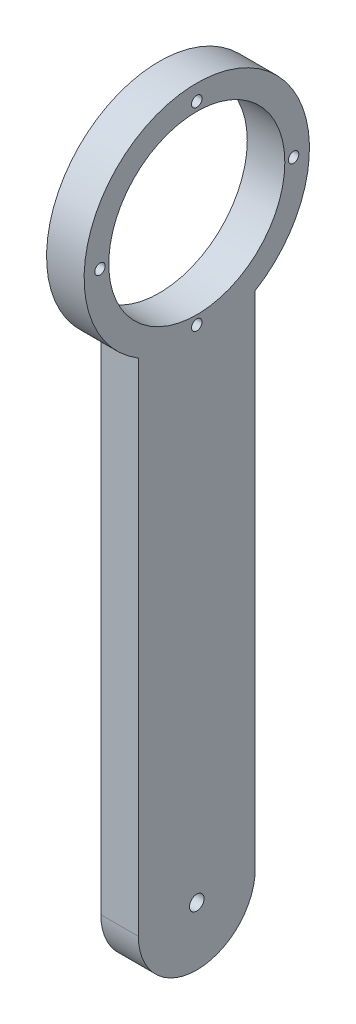
SolidWorks part; units mm, degrees
ref_plane "前视基准面" through (0, 0, 0) normal (0, 0, 1) x (1, 0, 0)
ref_plane "上视基准面" through (0, 0, 0) normal (0, 1, 0) x (1, 0, 0)
ref_plane "右视基准面" through (0, 0, 0) normal (1, 0, 0) x (0, 0, -1)
sketch "草图1" plane through (0, 0, 0) normal (1, 0, 0) x (0, 0, -1)
  line L2 (0, 0) -> (0, 120)
  line L4 (28, 0) -> (28, 120)
  arc A0 (0, 0) -> (28, 0) centre (14, 0) ccw
  arc A1 (28, 120) -> (0, 120) centre (14, 143.0868) ccw
  dimension "D3" = 27
  dimension "D1" = 28
  dimension "D2" = 120
extrude "凸台-拉伸6" add sketch "草图1" along normal blind 9
sketch "草图8" plane through (9, 0, 0) normal (1, 0, 0) x (0, 0, -1)
  circle A0 centre (14, 143.0868) radius 23.25
extrude "切除-拉伸6" cut sketch "草图8" against normal blind 7
sketch "草图9" plane through (2, 0, 0) normal (1, 0, 0) x (0, 0, -1)
  circle A0 centre (14, 143.0868) radius 19.25
extrude "切除-拉伸7" cut sketch "草图9" against normal blind 7
sketch "草图13" plane through (9, 0, 0) normal (1, 0, 0) x (0, 0, -1)
  circle A0 centre (14, 143.0868) radius 23.25
extrude "凸台-拉伸9" add sketch "草图13" against normal blind 9
sketch "草图14" plane through (9, 0, 0) normal (1, 0, 0) x (0, 0, -1)
  circle A0 centre (14, 143.0868) radius 21.1
  dimension "D1" = 42.2
sketch "草图15" plane through (9, 0, 0) normal (1, 0, 0) x (0, 0, -1)
extrude "切除-拉伸8" cut sketch "草图14" against normal blind 10
sketch "草图17" plane through (0, 0, 0) normal (-1, 0, 0) x (0, 0, 1)
  line L4 (0, 0) -> (0, 120)
  line L5 (-28, 120) -> (-28, 0)
  line L6 (0, 0) -> (0, 120)
  line L7 (-28, 120) -> (-28, 0)
  arc A4 (-28, 0) -> (0, 0) centre (-14, 0) ccw
  arc A5 (0, 120) -> (-28, 120) centre (-14, 143.0868) ccw
  arc A6 (-28, 0) -> (0, 0) centre (-14, 0) ccw
  arc A7 (0, 120) -> (-28, 120) centre (-14, 143.0868) ccw
  dimension "D1" = 0
sketch "草图25" plane through (0, 0, 0) normal (-1, 0, 0) x (0, 0, 1)
  circle A0 centre (9.2, 143.0868) radius 1.25
  circle A1 centre (-14, 119.8868) radius 1.25
  circle A2 centre (-37.2, 143.0868) radius 1.25
  circle A3 centre (-14, 166.2868) radius 1.25
  point P12 (-14, 143.0868)
  dimension "D1" = 4
  dimension "D3" = 2.5
  dimension "D2" = 23.2
sketch "草图26" plane through (9, 0, 0) normal (1, 0, 0) x (0, 0, -1)
  circle A0 centre (14, 0) radius 1.75
  dimension "D1" = 3.5
extrude "切除-拉伸14" cut sketch "草图26" against normal blind 10
extrude "切除-拉伸15" cut sketch "草图25" against normal blind 10
